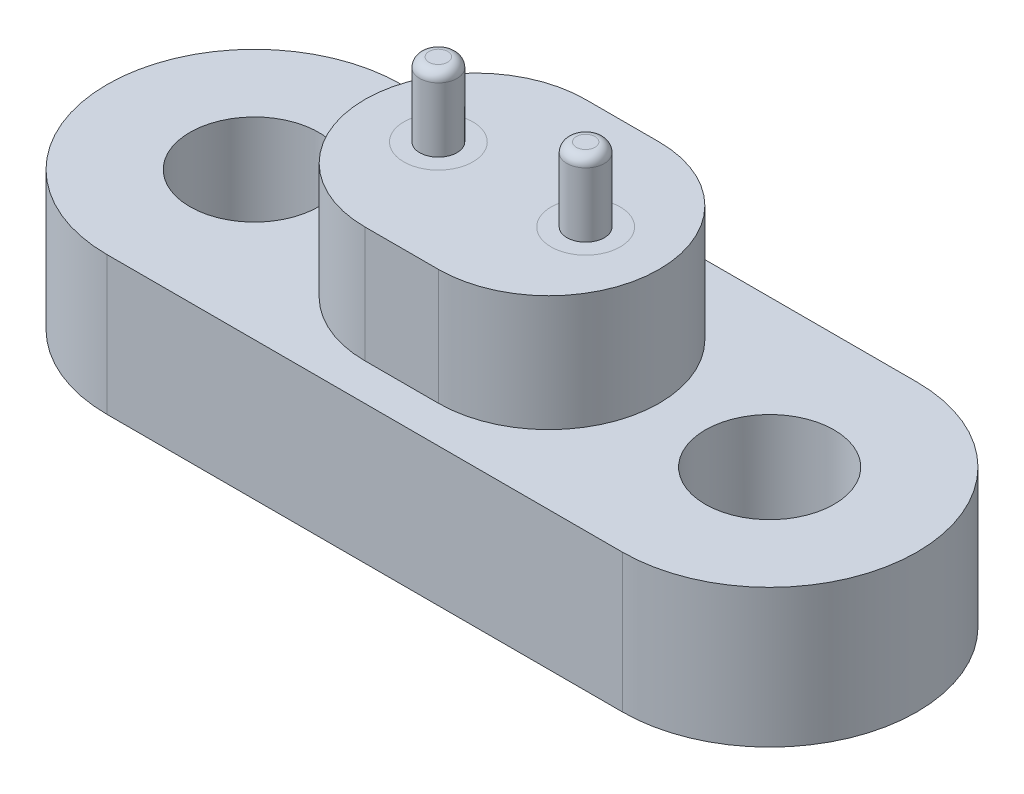
SolidWorks part; units mm, degrees
ref_plane "Front Plane" through (0, 0, 0) normal (0, 0, 1) x (1, 0, 0)
ref_plane "Top Plane" through (0, 0, 0) normal (0, 1, 0) x (1, 0, 0)
ref_plane "Right Plane" through (0, 0, 0) normal (1, 0, 0) x (0, 0, -1)
sketch "Sketch1" plane through (0, 0, 0) normal (0, 1, 0) x (1, 0, 0)
  line L0 (-6.999, 0) -> (6.999, 0) construction
  line L1 (-6.999, 4.0005) -> (6.999, 4.0005)
  line L2 (-6.999, -4.0005) -> (6.999, -4.0005)
  arc A0 (-6.999, 4.0005) -> (-6.999, -4.0005) centre (-6.999, 0) ccw
  arc A1 (6.999, -4.0005) -> (6.999, 4.0005) centre (6.999, 0) ccw
  point P2 (0, 0)
  dimension "D2" = 13.9979
  dimension "D1" = 8.001
extrude "Boss-Extrude1" add sketch "Sketch1" along normal blind 3.7592
sketch "Sketch2" plane through (0, 3.7592, 0) normal (0, 1, 0) x (1, 0, 0)
  line L0 (-1, 0) -> (1, 0) construction
  line L1 (-1, 2.9972) -> (1, 2.9972)
  line L2 (-1, -2.9972) -> (1, -2.9972)
  arc A0 (-1, 2.9972) -> (-1, -2.9972) centre (-1, 0) ccw
  arc A1 (1, -2.9972) -> (1, 2.9972) centre (1, 0) ccw
  circle A2 centre (-2.0002, 0) radius 0.9398
  circle A3 centre (2.0002, 0) radius 0.9398
  point P2 (0, 0)
  dimension "D2" = 1.8796
  dimension "D1" = 5.9944
  dimension "D3" = 2
extrude "Boss-Extrude2" add sketch "Sketch2" along normal blind 3.1496
sketch "Sketch3" plane through (0, 6.9088, 0) normal (0, 1, 0) x (1, 0, 0)
  circle A0 centre (-2.0002, 0) radius 0.9398
  circle A1 centre (2.0002, 0) radius 0.9398
extrude "Boss-Extrude3" add sketch "Sketch3" against normal blind 6.985 separate body
sketch "Sketch4" plane through (0, 6.9088, 0) normal (0, -1, 0) x (1, 0, 0)
  circle A0 centre (-2.0002, 0) radius 0.508
  circle A1 centre (2.0002, 0) radius 0.508
  dimension "D1" = 1.016
extrude "Boss-Extrude4" add sketch "Sketch4" against normal blind 2 separate body
fillet "Fillet1" radius 0.254 1 edges at (-2.0002, 8.9088, -0.508)
fillet "Fillet2" radius 0.254 1 edges at (2.0002, 8.9088, -0.508)
sketch "Sketch5" plane through (0, 3.7592, 0) normal (0, 1, 0) x (1, 0, 0)
  line L0 (0, 4.0005) -> (0, -4.0005) construction
  line L1 (6.999, 4.0005) -> (-6.999, 4.0005) construction
  line L2 (-6.999, -4.0005) -> (6.999, -4.0005) construction
  line L3 (-10.9995, 0) -> (10.9995, 0) construction
  circle A0 centre (-6.999, 0) radius 1.75
  arc A1 (-6.999, 4.0005) -> (-6.999, -4.0005) centre (-6.999, 0) ccw construction
  arc A2 (6.999, -4.0005) -> (6.999, 4.0005) centre (6.999, 0) ccw construction
  circle A3 centre (6.999, 0) radius 1.75
  dimension "D1" = 3.5
  dimension "D2" = 4.0005
extrude "Cut-Extrude1" cut sketch "Sketch5" against normal through all
